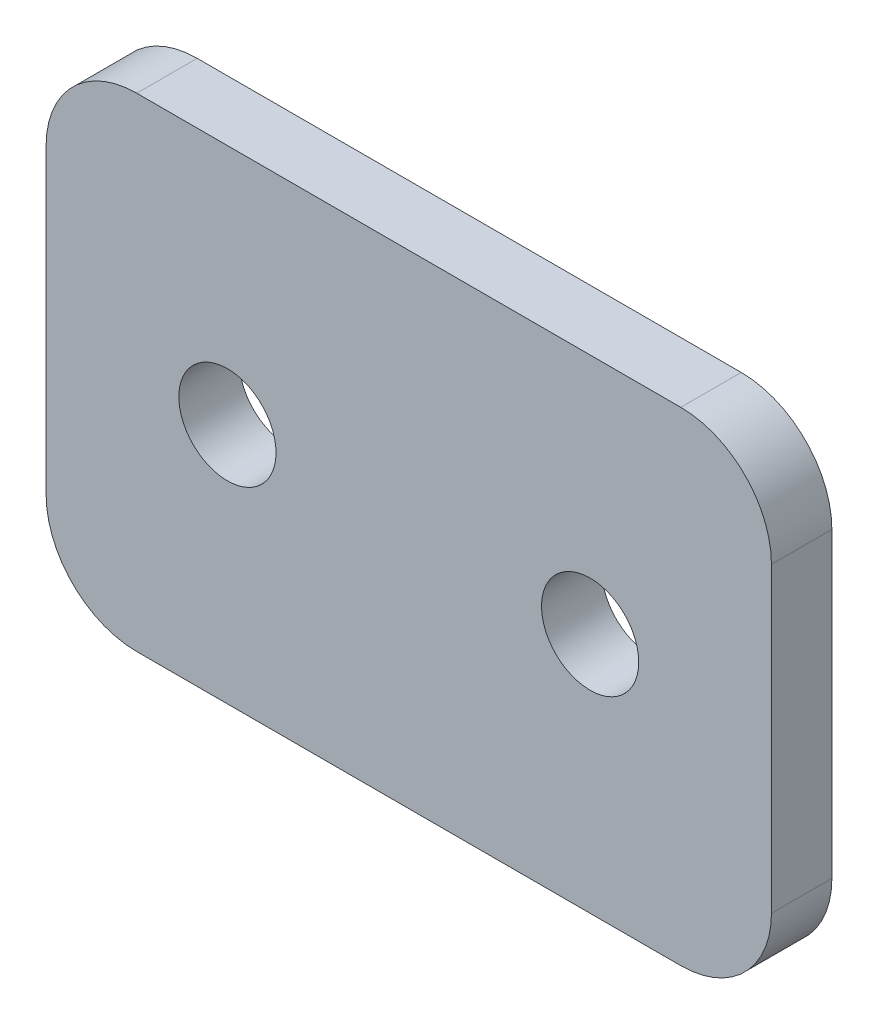
SolidWorks part; units mm, degrees
material "6061-T6 (SS)"
ref_plane "Front Plane" through (0, 0, 0) normal (0, 0, 1) x (1, 0, 0)
ref_plane "Top Plane" through (0, 0, 0) normal (0, 1, 0) x (1, 0, 0)
ref_plane "Right Plane" through (0, 0, 0) normal (1, 0, 0) x (0, 0, -1)
sketch "Sketch2" plane through (0, 0, 0) normal (0, 0, 1) x (1, 0, 0)
  line L1 (0, 0) -> (38.1, 0)
  line L2 (0, 0) -> (0, 25.4)
  line L3 (0, 25.4) -> (38.1, 25.4)
  line L4 (38.1, 0) -> (38.1, 25.4)
  circle A4 centre (9.525, 12.7) radius 2.5527
  circle A5 centre (28.575, 12.7) radius 2.5527
  point P12 (0, 12.7)
  dimension "D3" = 19.05
  dimension "D4" = 5.1054
  dimension "D1" = 25.4
  dimension "D2" = 38.1
  dimension ".375" = 9.525
extrude "Boss-Extrude1" add sketch "Sketch2" along normal blind 3.175
fillet "Fillet1" radius 4.7625 4 edges at (0, 25.4, 1.5875) (0, 0, 1.5875) (38.1, 0, 1.5875) (38.1, 25.4, 1.5875)
